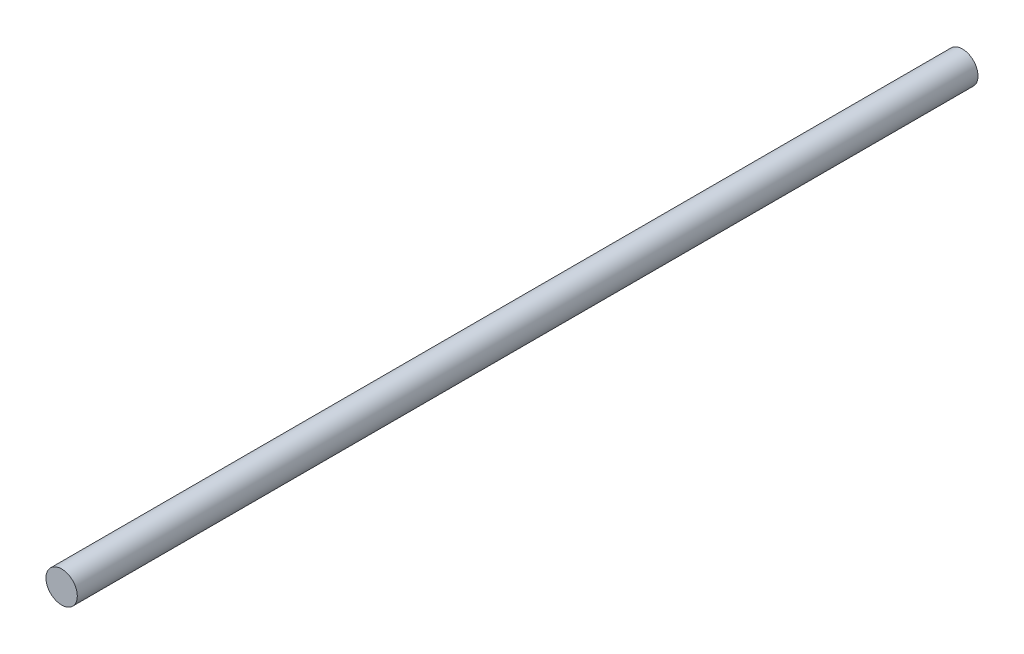
SolidWorks part; units mm, degrees
ref_plane "Front Plane" through (0, 0, 0) normal (0, 0, 1) x (1, 0, 0)
ref_plane "Top Plane" through (0, 0, 0) normal (0, 1, 0) x (1, 0, 0)
ref_plane "Right Plane" through (0, 0, 0) normal (1, 0, 0) x (0, 0, -1)
sketch "Sketch1" plane through (0, 0, 0) normal (0, 0, 1) x (1, 0, 0)
  circle A0 centre (-32.4004, 2.1188) radius 4
extrude "Boss-Extrude1" add sketch "Sketch1" along normal blind 230
